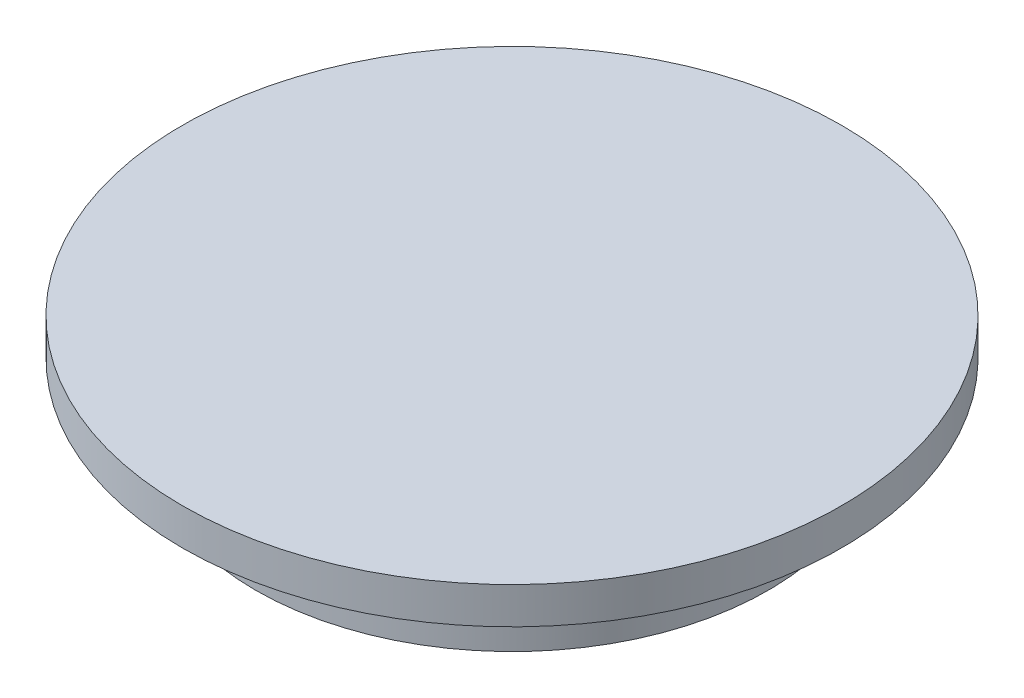
SolidWorks part; units mm, degrees
material "ABS PC"
ref_plane "Front Plane" through (0, 0, 0) normal (0, 0, 1) x (1, 0, 0)
ref_plane "Top Plane" through (0, 0, 0) normal (0, 1, 0) x (1, 0, 0)
ref_plane "Right Plane" through (0, 0, 0) normal (1, 0, 0) x (0, 0, -1)
sketch "Sketch1" plane through (0, 0, 0) normal (0, 1, 0) x (1, 0, 0)
  circle A0 centre (0, 0) radius 17.5
extrude "Boss-Extrude1" add sketch "Sketch1" along normal blind 5
sketch "Sketch2" plane through (0, 5, 0) normal (0, 1, 0) x (1, 0, 0)
  circle A0 centre (0, 0) radius 22.5
extrude "Boss-Extrude2" add sketch "Sketch2" along normal blind 2.5
